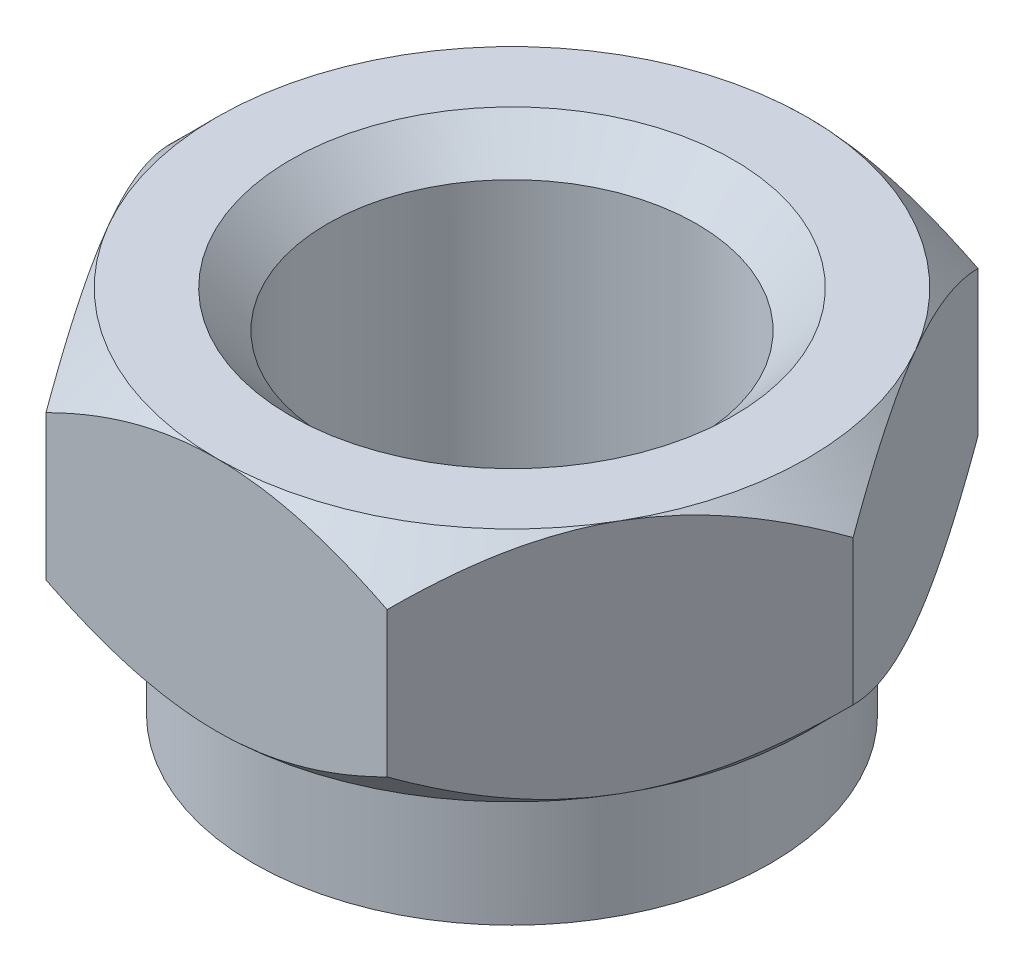
SolidWorks part; units mm, degrees
ref_plane "Płaszczyzna przednia" through (0, 0, 0) normal (0, 0, 1) x (1, 0, 0)
ref_plane "Płaszczyzna górna" through (0, 0, 0) normal (0, 1, 0) x (1, 0, 0)
ref_plane "Płaszczyzna prawa" through (0, 0, 0) normal (1, 0, 0) x (0, 0, -1)
sketch "Szkic1" plane through (0, 0, 0) normal (0, 1, 0) x (1, 0, 0)
  line L1 (4.6188, 0) -> (2.3094, 4)
  line L2 (2.3094, 4) -> (-2.3094, 4)
  line L3 (-2.3094, 4) -> (-4.6188, 0)
  line L4 (-4.6188, 0) -> (-2.3094, -4)
  line L5 (-2.3094, -4) -> (2.3094, -4)
  line L6 (2.3094, -4) -> (4.6188, 0)
  circle A0 centre (0, 0) radius 4 construction
  circle A1 centre (0, 0) radius 2.5
  dimension "D2" = 5
  dimension "D1" = 8
extrude "Dodanie-wyciągnięcie1" add sketch "Szkic1" along normal blind 3.2
sketch "Szkic2" plane through (0, 3.2, 0) normal (0, 1, 0) x (1, 0, 0)
  line L3 (2.3094, -4) -> (4.6188, 0) construction
  line L4 (2.3094, 4) -> (-2.3094, 4) construction
  line L5 (-4.6188, 0) -> (-2.3094, -4) construction
  circle A0 centre (0, 0) radius 4
extrude "Wytnij-wyciągnięcie29" cut sketch "Szkic2" against normal through all draft 45 flip side to cut contours A0
sketch "Szkic4" plane through (0, 0, 0) normal (0, -1, 0) x (-1, 0, 0)
  circle A0 centre (0, 0) radius 3.5
  circle A1 centre (0, 0) radius 2.5
  circle A2 centre (0, 0) radius 2.5 construction
  dimension "D1" = 7
extrude "Dodanie-wyciągnięcie2" add sketch "Szkic4" along normal blind 1.8
sketch "Szkic5" plane through (0, 0, 0) normal (0, -1, 0) x (-1, 0, 0)
  line L0 (2.3094, -4) -> (-2.3094, -4) construction
  circle A0 centre (0, 0) radius 4
extrude "Wytnij-wyciągnięcie30" cut sketch "Szkic5" against normal blind 10 draft 45 flip side to cut
fillet "Zaokrąglenie1" radius 0.1 1 edges at (0, 0, -3.5)
chamfer "Sfazowanie1" distance 0.5 angle 45 2 edges at (0, -1.8, -2.5) (0, 3.2, 2.5)
